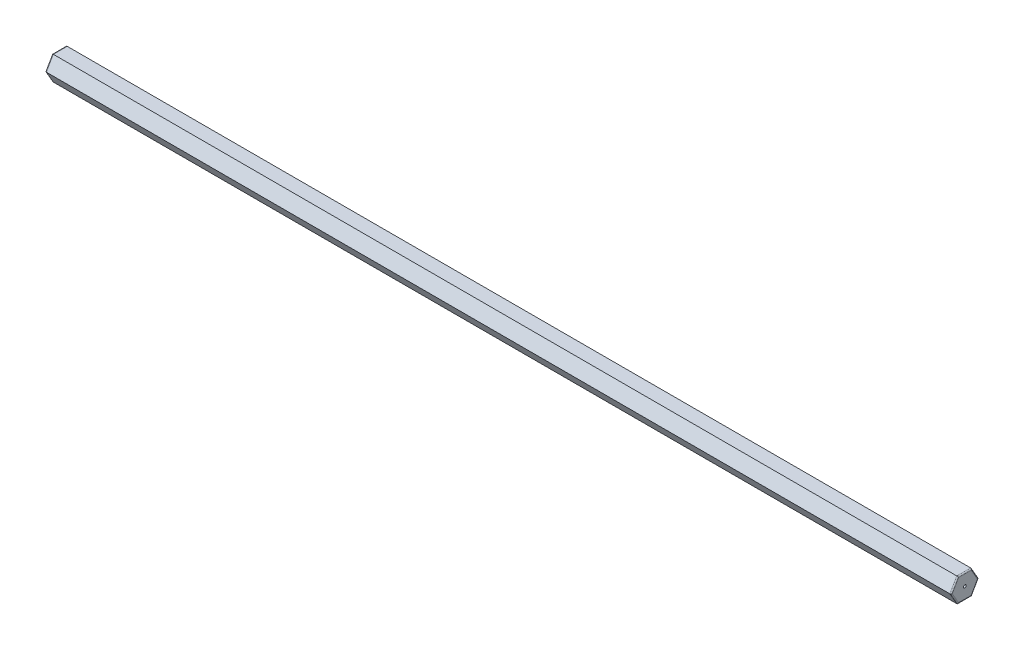
SolidWorks part; units mm, degrees
ref_plane "Front Plane" through (0, 0, 0) normal (0, 0, 1) x (1, 0, 0)
ref_plane "Top Plane" through (0, 0, 0) normal (0, 1, 0) x (1, 0, 0)
ref_plane "Right Plane" through (0, 0, 0) normal (1, 0, 0) x (0, 0, -1)
sketch "Sketch1" plane through (0, 0, 0) normal (1, 0, 0) x (0, 0, -1)
  line L1 (1.5398, 0) -> (0.7699, 1.3335)
  line L2 (0.7699, 1.3335) -> (-0.7699, 1.3335)
  line L3 (-0.7699, 1.3335) -> (-1.5398, 0)
  line L4 (-1.5398, 0) -> (-0.7699, -1.3335)
  line L5 (-0.7699, -1.3335) -> (0.7699, -1.3335)
  line L6 (0.7699, -1.3335) -> (1.5398, 0)
  circle A0 centre (0, 0) radius 1.3335 construction
  dimension "D1" = 2.667
extrude "Boss-Extrude1" add sketch "Sketch1" against normal blind 100.4824
fillet "Fillet1" radius 0.127 12 edges at (0, -0.6668, 1.1548) (0, -1.3335, 0) (0, -0.6668, -1.1548) (0, 0.6667, -1.1548) (0, 1.3335, 0) (0, 0.6668, 1.1548) (-100.4824, -1.3335, 0) (-100.4824, -0.6668, -1.1548) (-100.4824, 0.6667, -1.1548) (-100.4824, 1.3335, 0) (-100.4824, 0.6668, 1.1548) (-100.4824, -0.6668, 1.1548)
sketch "Sketch2" plane through (0, 0, 0) normal (1, 0, 0) x (0, 0, -1)
  circle A0 centre (0, 0) radius 0.1536
extrude "Cut-Extrude1" cut sketch "Sketch2" against normal blind 0.254
